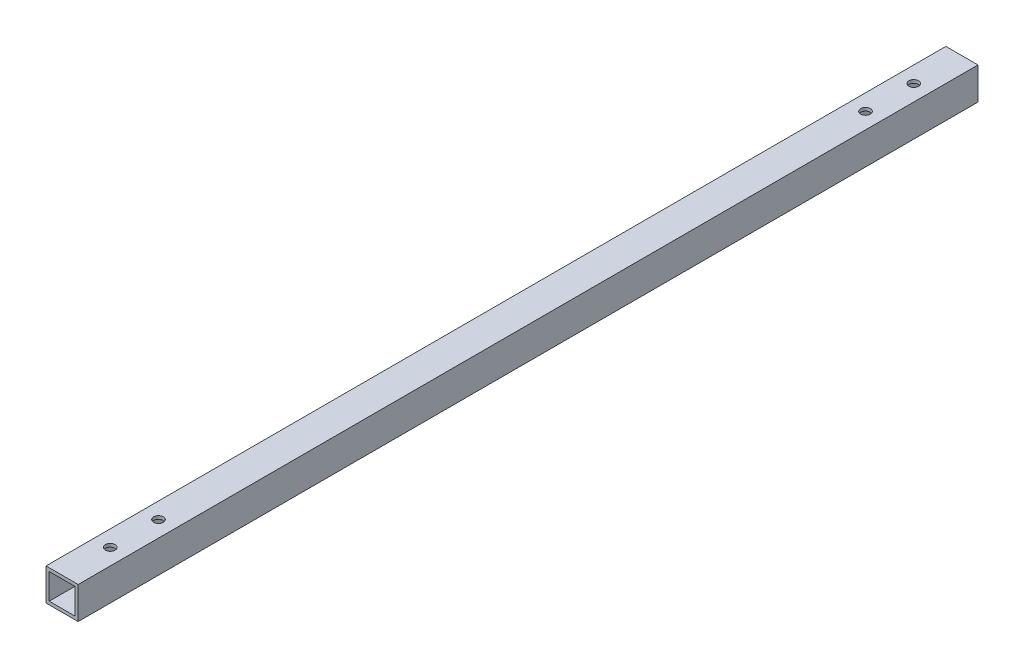
SolidWorks part; units mm, degrees
ref_plane "Front Plane" through (0, 0, 0) normal (0, 0, 1) x (1, 0, 0)
ref_plane "Top Plane" through (0, 0, 0) normal (0, 1, 0) x (1, 0, 0)
ref_plane "Right Plane" through (0, 0, 0) normal (1, 0, 0) x (0, 0, -1)
sketch "Sketch2" plane through (0, 0, 0) normal (0, 0, 1) x (1, 0, 0)
  line L5 (-5, 5) -> (5, 5)
  line L6 (-5, 5) -> (-5, -5)
  line L7 (-5, -5) -> (5, -5)
  line L8 (5, 5) -> (5, -5)
  line L9 (-5, 5) -> (5, -5) construction
  line L10 (-5, -5) -> (5, 5) construction
  line L11 (-4, 4) -> (4, 4)
  line L12 (-4, 4) -> (-4, -4)
  line L13 (-4, -4) -> (4, -4)
  line L14 (4, 4) -> (4, -4)
  line L15 (-4, 4) -> (4, -4) construction
  line L16 (-4, -4) -> (4, 4) construction
  point P0 (0, 0)
  point P6 (0, 0)
  dimension "D1" = 10
  dimension "D2" = 10
  dimension "D3" = 8
  dimension "D4" = 8
extrude "Boss-Extrude1" add sketch "Sketch2" along normal blind 280
sketch "Sketch3" plane through (0, 5, 0) normal (0, 1, 0) x (1, 0, 0)
  line L0 (5, -280) -> (-5, -280) construction
  circle A0 centre (0, -15) radius 1.5
  circle A1 centre (0, -30) radius 1.5
  circle A2 centre (0, -265) radius 1.5
  circle A3 centre (0, -250) radius 1.5
  dimension "D3" = 3
  dimension "D4" = 3
  dimension "D5" = 3
  dimension "D7" = 15
  dimension "D1" = 15
  dimension "D2" = 15
  dimension "D6" = 15
extrude "Cut-Extrude1" cut sketch "Sketch3" against normal blind 28
